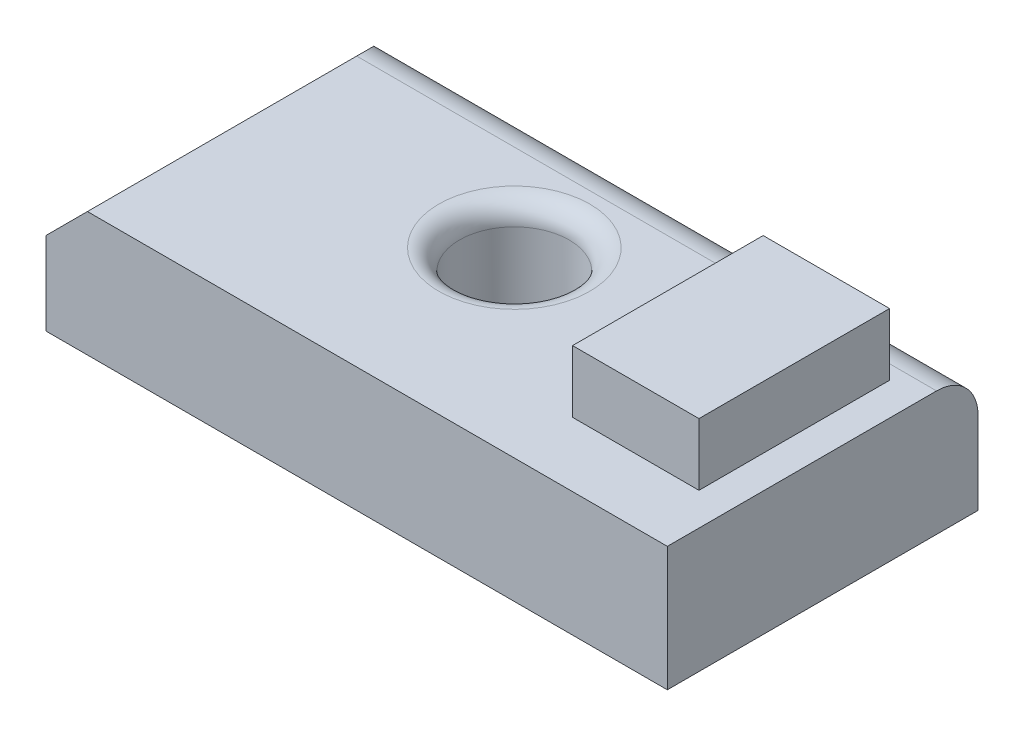
SolidWorks part; units mm, degrees
ref_plane "Front Plane" through (0, 0, 0) normal (0, 0, 1) x (1, 0, 0)
ref_plane "Top Plane" through (0, 0, 0) normal (0, 1, 0) x (1, 0, 0)
ref_plane "Right Plane" through (0, 0, 0) normal (1, 0, 0) x (0, 0, -1)
sketch "Sketch1" plane through (0, 0, 0) normal (0, 1, 0) x (1, 0, 0)
  line L4 (-342.3733, 1128.076) -> (3467.6267, 1128.076)
  line L5 (-342.3733, 1128.076) -> (-342.3733, -776.924)
  line L6 (-342.3733, -776.924) -> (3467.6267, -776.924)
  line L7 (3467.6267, 1128.076) -> (3467.6267, -776.924)
  dimension "D1" = 3810
  dimension "D2" = 1905
extrude "Boss-Extrude1" add sketch "Sketch1" along normal blind 762 contours L5 L4 L7 L6
sketch "Sketch2" plane through (0, 762, 0) normal (0, 1, 0) x (1, 0, 0)
  circle A0 centre (1412.4667, 339.9404) radius 336.2582
extrude "Cut-Extrude1" cut sketch "Sketch2" against normal through all
sketch "Sketch3" plane through (0, 762, 0) normal (0, 1, 0) x (1, 0, 0)
  line L9 (2491.9956, 786.3621) -> (3267.146, 786.3621)
  line L10 (2491.9956, 786.3621) -> (2491.9956, -382.4511)
  line L11 (2491.9956, -382.4511) -> (3267.146, -382.4511)
  line L12 (3267.146, 786.3621) -> (3267.146, -382.4511)
extrude "Boss-Extrude2" add sketch "Sketch3" along normal blind 381
fillet "Fillet1" radius 127 1 edges at (1412.4667, 762, -3.6822)
chamfer "Chamfer3" distance 254 angle 45 1 edges at (-342.3733, 381, -1128.076)
fillet "Fillet3" radius 254 1 edges at (1689.6267, 762, -1128.076)
chamfer "Chamfer4" distance 254 angle 45 1 edges at (-342.3733, 762, -48.576)
